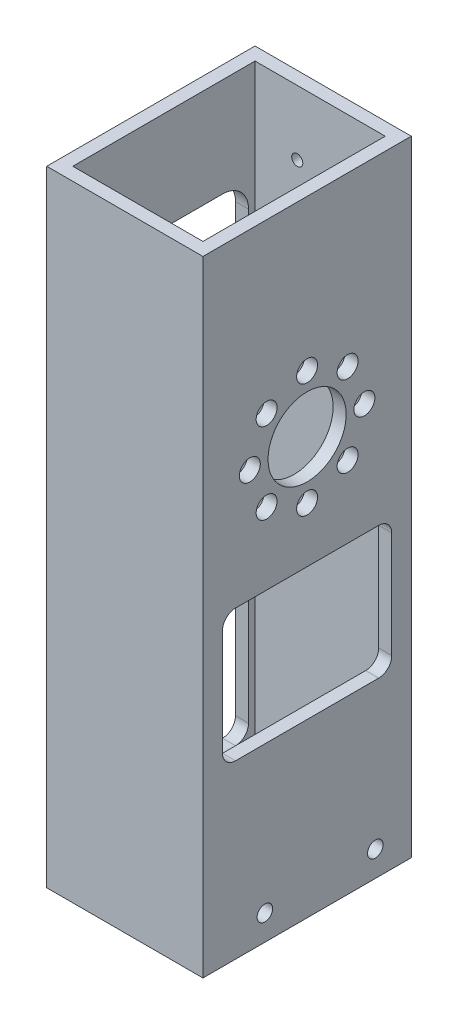
SolidWorks part; units mm, degrees
material "6061 Alloy"
ref_plane "Front" through (0, 0, 0) normal (0, 0, 1) x (1, 0, 0)
ref_plane "Top" through (0, 0, 0) normal (0, 1, 0) x (1, 0, 0)
ref_plane "Right" through (0, 0, 0) normal (1, 0, 0) x (0, 0, -1)
sketch "Sketch1" plane through (0, 0, 0) normal (0, 1, 0) x (1, 0, 0)
  line L0 (-15.875, 22.225) -> (15.875, 22.225)
  line L1 (-19.05, -25.4) -> (19.05, -25.4)
  line L2 (-19.05, -25.4) -> (-19.05, 25.4)
  line L3 (-19.05, 25.4) -> (19.05, 25.4)
  line L4 (19.05, -25.4) -> (19.05, 25.4)
  line L5 (-19.05, -25.4) -> (19.05, 25.4) construction
  line L6 (-19.05, 25.4) -> (19.05, -25.4) construction
  line L7 (15.875, -22.225) -> (15.875, 22.225)
  line L8 (-15.875, -22.225) -> (15.875, -22.225)
  line L9 (-15.875, -22.225) -> (-15.875, 22.225)
  point P0 (0, 0)
  dimension "D1" = 38.1
  dimension "D2" = 50.8
  dimension "D3" = 3.175
extrude "Boss-Extrude1" add sketch "Sketch1" along normal blind 152.4
sketch "Sketch2" plane through (15.875, 0, 0) normal (-1, 0, 0) x (0, 0, 1)
  circle A0 centre (-16.6454, 6.2154) radius 1.8986
  circle A1 centre (10.3003, 6.1824) radius 1.8986
  dimension "D1" = 3.7973
extrude "Cut-Extrude1" cut sketch "Sketch2" against normal through all both and the other way through all
sketch "Sketch4" plane through (-19.05, 0, 0) normal (-1, 0, 0) x (0, 0, 1)
  line L0 (-25.4, 152.4) -> (-25.4, 0) construction
  line L1 (17.4625, 10.16) -> (-17.4625, 10.16)
  line L2 (20.6375, 13.335) -> (20.6375, 64.135)
  line L3 (17.4625, 67.31) -> (-17.4625, 67.31)
  line L4 (-20.6375, 13.335) -> (-20.6375, 64.135)
  line L5 (20.6375, 10.16) -> (-20.6375, 67.31) construction
  line L6 (20.6375, 67.31) -> (-20.6375, 10.16) construction
  line L7 (25.4, 152.4) -> (25.4, 0) construction
  line L8 (-25.4, 0) -> (25.4, 0) construction
  arc A0 (-17.4625, 67.31) -> (-20.6375, 64.135) centre (-17.4625, 64.135) ccw
  arc A1 (20.6375, 64.135) -> (17.4625, 67.31) centre (17.4625, 64.135) ccw
  arc A2 (17.4625, 10.16) -> (20.6375, 13.335) centre (17.4625, 13.335) ccw
  arc A3 (-17.4625, 10.16) -> (-20.6375, 13.335) centre (-17.4625, 13.335) cw
  point P4 (0, 38.735)
  dimension "D4" = 3.175
  dimension "D1" = 4.7625
  dimension "D2" = 4.7625
  dimension "D3" = 10.16
  dimension "D5" = 57.15
extrude "Cut-Extrude3" cut sketch "Sketch4" against normal blind 3.175
sketch "Sketch5" plane through (19.05, 0, 0) normal (1, 0, 0) x (0, 0, -1)
  line L0 (25.4, 152.4) -> (25.4, 0) construction
  line L1 (17.4625, 67.31) -> (-17.4625, 67.31)
  line L2 (20.6375, 64.135) -> (20.6375, 45.085)
  line L3 (17.4625, 41.91) -> (-17.4625, 41.91)
  line L4 (-20.6375, 64.135) -> (-20.6375, 45.085)
  line L5 (20.6375, 67.31) -> (-20.6375, 41.91) construction
  line L6 (20.6375, 41.91) -> (-20.6375, 67.31) construction
  line L7 (-25.4, 152.4) -> (-25.4, 0) construction
  line L10 (25.4, 0) -> (-25.4, 0) construction
  arc A0 (-17.4625, 41.91) -> (-20.6375, 45.085) centre (-17.4625, 45.085) cw
  arc A1 (-17.4625, 67.31) -> (-20.6375, 64.135) centre (-17.4625, 64.135) ccw
  arc A2 (20.6375, 45.085) -> (17.4625, 41.91) centre (17.4625, 45.085) cw
  arc A3 (17.4625, 67.31) -> (20.6375, 64.135) centre (17.4625, 64.135) cw
  point P4 (0, 54.61)
  dimension "D5" = 3.175
  dimension "D1" = 4.7625
  dimension "D2" = 4.7625
  dimension "D3" = 67.31
  dimension "D4" = 25.4
extrude "Cut-Extrude4" cut sketch "Sketch5" against normal blind 3.175
sketch "Sketch6" plane through (15.875, 0, 0) normal (-1, 0, 0) x (0, 0, 1)
  line L0 (0, 101.6) -> (0, 0) construction
  line L1 (0, 87.63) -> (0, 101.6) construction
  circle A0 centre (0, 101.6) radius 9.525
  circle A1 centre (0, 87.63) radius 2.5527
  circle A2 centre (-9.8783, 91.7217) radius 2.5527
  circle A3 centre (-13.97, 101.6) radius 2.5527
  circle A4 centre (-9.8783, 111.4783) radius 2.5527
  circle A5 centre (0, 115.57) radius 2.5527
  circle A6 centre (9.8783, 111.4783) radius 2.5527
  circle A7 centre (13.97, 101.6) radius 2.5527
  circle A8 centre (9.8783, 91.7217) radius 2.5527
  point P22 (0, 101.6)
  dimension "D1" = 19.05
  dimension "D3" = 5.1054
  dimension "D2" = 101.6
  dimension "D4" = 13.97
  dimension "D6" = 0
  dimension "D5" = 8
extrude "Cut-Extrude5" cut sketch "Sketch6" against normal blind 3.175
sketch "Sketch7" plane through (-19.05, 0, 0) normal (-1, 0, 0) x (0, 0, 1)
  line L0 (25.4, 152.4) -> (25.4, 0) construction
  line L1 (-14.2875, 77.47) -> (14.2875, 77.47)
  line L2 (-20.6375, 83.82) -> (-20.6375, 121.92)
  line L3 (-14.2875, 128.27) -> (14.2875, 128.27)
  line L4 (20.6375, 83.82) -> (20.6375, 121.92)
  line L5 (-20.6375, 77.47) -> (20.6375, 128.27) construction
  line L6 (-20.6375, 128.27) -> (20.6375, 77.47) construction
  line L7 (-25.4, 152.4) -> (-25.4, 0) construction
  line L8 (16.51, 67.31) -> (-16.51, 67.31) construction
  arc A0 (-20.6375, 121.92) -> (-14.2875, 128.27) centre (-14.2875, 121.92) cw
  arc A1 (14.2875, 128.27) -> (20.6375, 121.92) centre (14.2875, 121.92) cw
  arc A2 (14.2875, 77.47) -> (20.6375, 83.82) centre (14.2875, 83.82) ccw
  arc A3 (-14.2875, 77.47) -> (-20.6375, 83.82) centre (-14.2875, 83.82) cw
  point P4 (0, 102.87)
  dimension "D5" = 6.35
  dimension "D1" = 50.8
  dimension "D2" = 4.7625
  dimension "D3" = 4.7625
  dimension "D4" = 10.16
extrude "Cut-Extrude6" cut sketch "Sketch7" against normal blind 3.175
sketch "Sketch11" plane through (0, 0, -25.4) normal (0, 0, -1) x (-1, 0, 0)
  line L0 (-5.5796, 136.6393) -> (5.5796, 136.6393) construction
  line L1 (0, 136.6393) -> (0, 152.4) construction
  line L2 (-19.05, 152.4) -> (19.05, 152.4) construction
hole_wizard "#6-32 Tapped Hole2" positions "3DSketch2" profile "Sketch12" tap size "#6-32" standard "ANSI Inch" end condition up to next
sketch3d "3DSketch2"
  point P0 (5.5796, 136.6393, -25.4)
  point P3 (-5.5796, 136.6393, -25.4)
cosmetic thread "Hole Thread1" parameters "D2"=3.5052
cosmetic thread "Hole Thread2" parameters "D2"=3.5052
sketch "Sketch12" plane through (5.5796, 136.6393, -25.4) normal (1, 0, 0) x (0, 1, 0)
  line L0 (0, 0) -> (0, 3.175)
  line L1 (0, 3.175) -> (1.3525, 3.175)
  line L2 (1.3525, 3.175) -> (1.3525, 0)
  line L5 (1.3525, 0) -> (0, 0)
  line L11 (0, -6.35) -> (0, 107.95) construction
  dimension "Thru Tap Drill Dia." = 2.7051
  dimension "Thru Tap Drill Depth" = 3.175
sketch "Sketch13" plane through (19.05, 0, 0) normal (1, 0, 0) x (0, 0, -1)
  line L2 (0, 78.486) -> (20.6375, 78.486)
  line L3 (20.6375, 78.486) -> (20.6375, 64.135)
  line L4 (0, 78.486) -> (-20.6375, 78.486)
  line L5 (-20.6375, 78.486) -> (-20.6375, 64.135)
  line L6 (20.6375, 64.135) -> (-20.6375, 64.135)
extrude "Cut-Extrude7" cut sketch "Sketch13" against normal up to next and the other way through all contours L3 L6 L5 L4 L2
fillet "Fillet1" radius 3.175 1 edges at (17.4625, 78.486, -20.6375)
fillet "Fillet2" radius 3.175 1 edges at (17.4625, 78.486, 20.6375)
sketch "Sketch15" plane through (-19.05, 0, 0) normal (-1, 0, 0) x (0, 0, 1)
  line L0 (0, 67.31) -> (0, 78.486) construction
  line L1 (17.4625, 67.31) -> (-17.4625, 67.31) construction
  line L2 (0, 78.486) -> (0, 88.646) construction
  line L3 (0, 78.486) -> (-20.6375, 78.486)
  line L4 (0, 78.486) -> (20.6375, 78.486)
  line L5 (0, 88.646) -> (20.6375, 88.646)
  line L6 (20.6375, 83.82) -> (20.6375, 121.92) construction
  line L7 (20.6375, 88.646) -> (20.6375, 78.486)
  line L8 (0, 88.646) -> (-20.6375, 88.646)
  line L9 (-20.6375, 121.92) -> (-20.6375, 83.82) construction
  line L10 (-20.6375, 88.646) -> (-20.6375, 78.486)
  dimension "D1" = 11.176
  dimension "D2" = 10.16
extrude "Boss-Extrude2" add sketch "Sketch15" against normal blind 3.175
sketch "Sketch16" plane through (-19.05, 0, 0) normal (-1, 0, 0) x (0, 0, 1)
  line L0 (0, 78.486) -> (20.6375, 78.486)
  line L1 (-17.7329, 78.486) -> (17.7329, 78.486) construction
  line L2 (20.6375, 78.486) -> (20.6375, 64.135)
  line L3 (20.6375, 64.135) -> (-20.6375, 64.135)
  line L4 (-20.6375, 64.135) -> (-20.6375, 78.486)
  line L5 (-20.6375, 78.486) -> (0, 78.486)
extrude "Cut-Extrude8" cut sketch "Sketch16" against normal up to next
fillet "Fillet3" radius 3.175 1 edges at (-17.4625, 78.486, 20.6375)
fillet "Fillet4" radius 3.175 1 edges at (-17.4625, 78.486, -20.6375)
fillet "Fillet5" radius 6.35 1 edges at (-17.4625, 88.646, -20.6375)
fillet "Fillet6" radius 6.35 1 edges at (-17.4625, 88.646, 20.6375)
sketch "Sketch17" plane through (-19.05, 0, 0) normal (-1, 0, 0) x (0, 0, 1)
  line L0 (0, 78.486) -> (0, 74.168) construction
  line L1 (-17.4625, 78.486) -> (17.4625, 78.486) construction
  line L2 (0, 74.168) -> (20.6375, 74.168)
  line L3 (20.6375, 13.335) -> (20.6375, 75.311) construction
  line L4 (20.6375, 74.168) -> (20.6375, 84.3547)
  line L5 (20.6375, 84.3547) -> (-20.6375, 84.3547)
  line L6 (-20.6375, 84.3547) -> (-20.6375, 74.168)
  line L7 (-20.6375, 75.311) -> (-20.6375, 13.335) construction
  line L8 (-20.6375, 74.168) -> (0, 74.168)
  dimension "D1" = 4.318
extrude "Boss-Extrude3" add sketch "Sketch17" against normal blind 3.175
sketch "Sketch18" plane through (-19.05, 0, 0) normal (-1, 0, 0) x (0, 0, 1)
  line L0 (0, 74.168) -> (0, 84.328) construction
  line L1 (-20.6375, 74.168) -> (20.6375, 74.168) construction
  line L2 (0, 84.328) -> (-20.6375, 84.328)
  line L3 (-20.6375, 84.328) -> (-20.6375, 94.996)
  line L4 (-20.6375, 94.996) -> (20.6375, 94.996)
  line L5 (20.6375, 94.996) -> (20.6375, 84.328)
  line L6 (20.6375, 84.328) -> (0, 84.328)
  dimension "D1" = 10.16
extrude "Cut-Extrude9" cut sketch "Sketch18" against normal up to next
sketch "Sketch19" plane through (19.05, 0, 0) normal (1, 0, 0) x (0, 0, -1)
  line L0 (0, 78.486) -> (0, 74.168) construction
  line L1 (17.4625, 78.486) -> (-17.4625, 78.486) construction
  line L2 (0, 74.168) -> (20.6375, 74.168)
  line L3 (20.6375, 45.085) -> (20.6375, 75.311) construction
  line L4 (20.6375, 74.168) -> (20.6375, 78.486)
  line L5 (20.6375, 78.486) -> (-20.6375, 78.486)
  line L6 (0, 74.168) -> (-20.6375, 74.168)
  line L7 (-20.6375, 75.311) -> (-20.6375, 45.085) construction
  line L8 (-20.6375, 74.168) -> (-20.6375, 78.486)
  dimension "D1" = 4.318
extrude "Boss-Extrude4" add sketch "Sketch19" against normal blind 3.175
fillet "Fillet7" radius 3.175 1 edges at (17.4625, 74.168, -20.6375)
fillet "Fillet8" radius 3.175 1 edges at (17.4625, 74.168, 20.6375)
fillet "Fillet9" radius 3.175 1 edges at (-17.4625, 74.168, 20.6375)
fillet "Fillet10" radius 3.175 1 edges at (-17.4625, 74.168, -20.6375)
fillet "Fillet11" radius 6.35 1 edges at (-17.4625, 84.328, -20.6375)
fillet "Fillet12" radius 6.35 1 edges at (-17.4625, 84.328, 20.6375)
